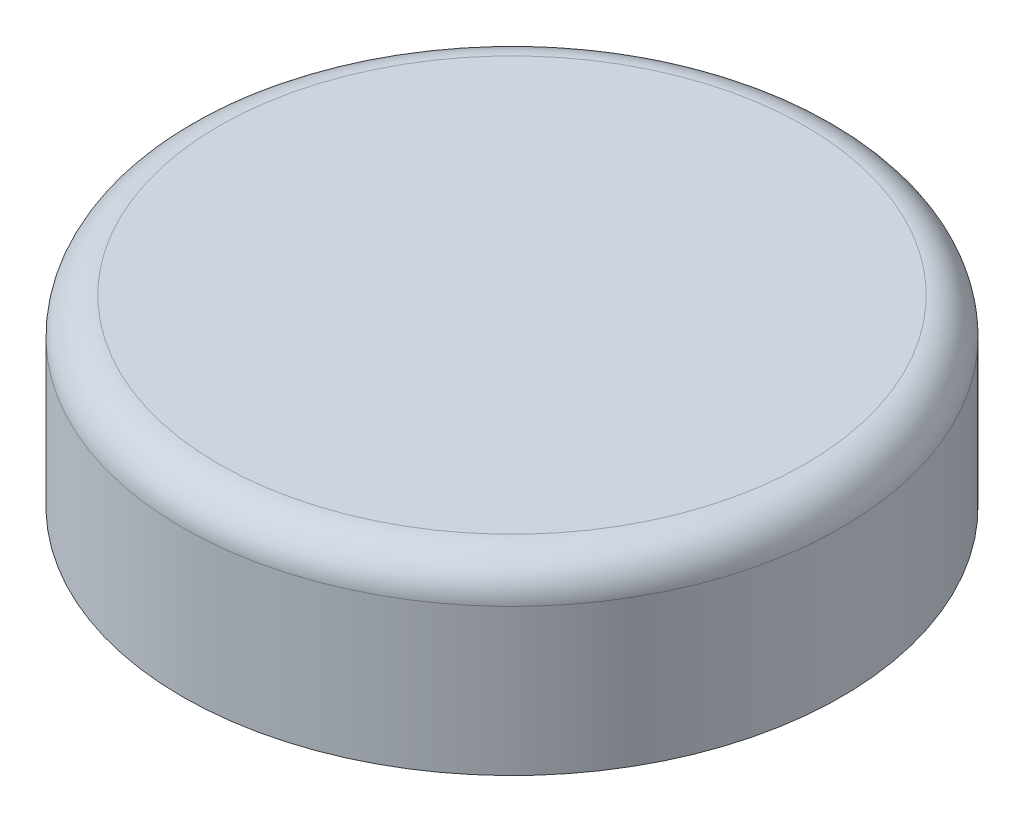
SolidWorks part; units mm, degrees
ref_plane "Plan de face" through (0, 0, 0) normal (0, 0, 1) x (1, 0, 0)
ref_plane "Plan de dessus" through (0, 0, 0) normal (0, 1, 0) x (1, 0, 0)
ref_plane "Plan de droite" through (0, 0, 0) normal (1, 0, 0) x (0, 0, -1)
sketch "Esquisse1" plane through (0, 0, 0) normal (0, 1, 0) x (1, 0, 0)
  circle A0 centre (0, 0) radius 9
  dimension "D1" = 18
extrude "Boss.-Extru.1" add sketch "Esquisse1" along normal blind 5
fillet "Congé1" radius 1 1 edges at (0, 5, 9)
